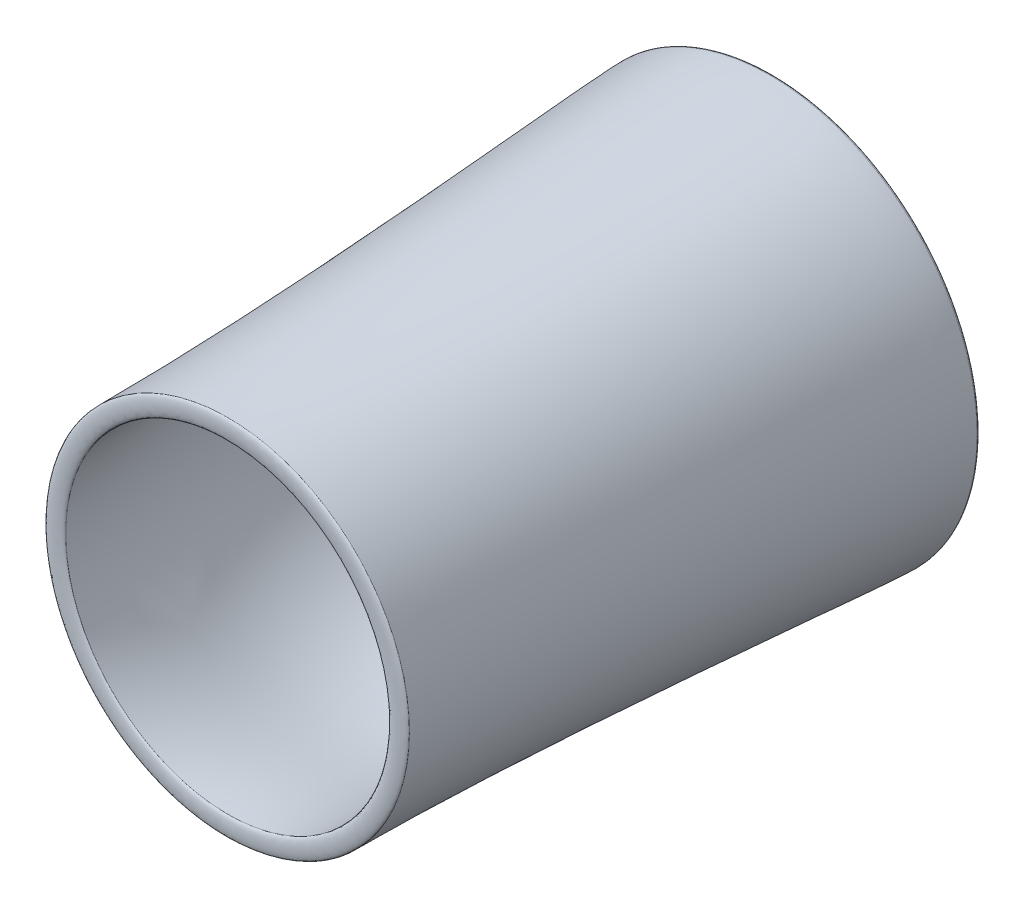
SolidWorks part; units mm, degrees
ref_plane "Front Plane" through (0, 0, 0) normal (0, 0, 1) x (1, 0, 0)
ref_plane "Top Plane" through (0, 0, 0) normal (0, 1, 0) x (1, 0, 0)
ref_plane "Right Plane" through (0, 0, 0) normal (1, 0, 0) x (0, 0, -1)
sketch "Sketch1" plane through (0, 0, 0) normal (0, 0, 1) x (1, 0, 0)
  circle A0 centre (0, 0) radius 50.8
  dimension "D1" = 101.6
ref_plane "Plane1" through (0, -254, 0) normal (0, 1, 0) x (1, 0, 0)
sketch "Sketch6" plane through (0, 0, 0) normal (0, 1, 0) x (1, 0, 0)
  line L0 (0, -99.6848) -> (0, 145.6048) construction
ref_plane "Plane2" through (0, -114.3, 0) normal (0, 1, 0) x (1, 0, 0)
sketch "Sketch12" plane through (0, 0, 0) normal (0, 1, 0) x (1, 0, 0)
  line L0 (0, -1104.7568) -> (0, -908.6135) construction
ref_plane "Plane3" through (0, 0, 203.2) normal (0, 0, 1) x (1, 0, 0)
ref_plane "Plane4" through (0, 0, 889) normal (0, 0, 1) x (1, 0, 0)
sketch "Sketch17" plane through (0, 0, 0) normal (0, 1, 0) x (1, 0, 0)
  line L0 (-259.4955, -43.5301) -> (-259.4955, 70.1436) construction
  line L1 (-110.6437, -1316.1124) -> (-110.6437, -853.5386) construction
  line L2 (-259.4955, 45.4622) -> (-387.328, 45.4622)
  line L3 (-387.328, 45.4622) -> (-387.328, -1084.8928)
  line L4 (-387.328, -1084.8928) -> (-110.6437, -1084.8928)
  spline S0 degree 3 poles (-259.4955, 45.4622) (-259.4955, -7.1736) (-207.7477, -105.8122) (-173.3147, -383.1384) (-92.4228, -818.9689) (-110.6437, -795.7842) (-110.6437, -1084.8928) knots 0 0 0 0 0.158009 0.206507 0.484977 1 1 1 1
sketch "Sketch21" plane through (0, 0, 0) normal (0, 1, 0) x (1, 0, 0)
  line L0 (-711.6099, -22.8536) -> (-711.6099, 113.778) construction
  line L1 (-623.0819, -1315.9117) -> (-623.0819, -853.874) construction
  line L2 (-663.0656, 561.8781) -> (-711.6099, 561.8781) construction
  line L3 (-556.6317, -1297.8221) -> (-623.0819, -1297.8221) construction
  line L4 (-556.6317, -1297.8221) -> (-623.0819, -1297.8221)
  line L6 (-663.0656, 561.8781) -> (-711.6099, 561.8781)
  spline S0 degree 3 poles (-663.0656, 561.8781) (-663.0656, 509.2424) (-605.3156, 116.4208) (-570.3602, -82.5554) (-651.1086, -812.7061) (-556.6317, -1008.7135) (-556.6317, -1297.8221) knots 0 0 0 0 0.158009 0.206507 0.484977 1 1 1 1
  spline S1 degree 3 poles (-711.6099, 561.8781) (-711.6099, 436.4942) (-623.0819, -567.513) (-623.0819, -1297.8221) knots 0 0 0 0 1 1 1 1
  point P10 (-409.5735, -1093.4611)
  point P11 (-450.1433, -301.8798)
  point P12 (-623.0819, -1308.9952)
  point P13 (-556.6317, -1297.8221)
  point P14 (-500.9926, -321.0274)
  point P15 (-594.2974, 54.138)
  point P16 (0, 0)
  point P17 (-663.0656, 561.8781)
  point P18 (-607.4148, -546.9689)
revolve "Revolve2" add sketch "Sketch21" angle 360 about L0
sketch "Sketch22" plane through (0, 0, 0) normal (0, 1, 0) x (1, 0, 0)
  line L0 (-711.6099, 561.8781) -> (-663.0656, 561.8781)
  line L1 (-663.0656, 558.0691) -> (-663.0656, 565.6872) construction
  line L2 (-711.6099, 563.2709) -> (-711.6099, 560.4854) construction
  spline S0 degree 3 poles (-711.6099, 561.8781) (-711.6099, 578.8115) (-663.0656, 578.8115) (-663.0656, 561.8781) knots 0 0 0 0 1 1 1 1
revolve "Revolve3" add sketch "Sketch22" angle 360 about L0
sketch "Sketch23" plane through (0, 0, 0) normal (0, 1, 0) x (1, 0, 0)
  line L0 (-623.0819, -1297.8221) -> (-556.6317, -1297.8221)
  line L1 (-623.0819, -1307.0332) -> (-623.0819, -1288.6111) construction
  line L2 (-556.6317, -1287.2491) -> (-556.6317, -1308.3952) construction
  spline S0 degree 3 poles (-623.0819, -1297.8221) (-623.0819, -1310.5221) (-556.6317, -1310.5221) (-556.6317, -1297.8221) knots 0 0 0 0 1 1 1 1
revolve "Revolve4" add sketch "Sketch23" angle 360 about L0
ref_plane "Plane5" through (289.9098, 0, 0) normal (1, 0, 0) x (0, 0, -1)
sketch "Sketch24" plane through (289.9098, 0, 0) normal (1, 0, 0) x (0, 0, -1)
  line L0 (-1123.5724, -17.6357) -> (119.2276, -17.6357) construction
  line L1 (-1297.8221, 0) -> (561.8781, 0) construction
  line L2 (-1297.8221, -623.0819) -> (-1297.8221, 623.0819) construction
  line L3 (561.8781, 711.6099) -> (561.8781, -711.6099) construction
  text T0 "MD-130 Gas Turbine Engine" font "TI-Nspire" height in points 160
